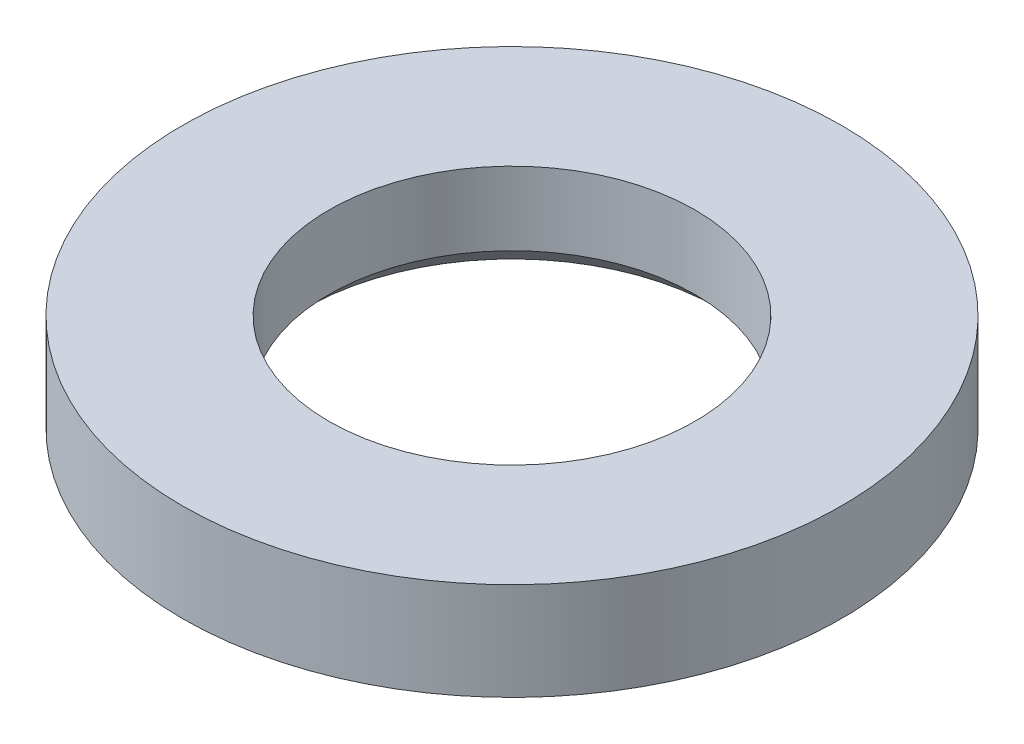
SolidWorks part; units mm, degrees
ref_plane "Front Plane" through (0, 0, 0) normal (0, 0, 1) x (1, 0, 0)
ref_plane "Top Plane" through (0, 0, 0) normal (0, 1, 0) x (1, 0, 0)
ref_plane "Right Plane" through (0, 0, 0) normal (1, 0, 0) x (0, 0, -1)
sketch "Sketch1" plane through (0, 0, 0) normal (0, 0, 1) x (1, 0, 0)
  line L0 (1.5, 0) -> (2.7, 0)
  line L1 (2.7, 0) -> (2.7, 0.8)
  line L2 (2.7, 0.8) -> (1.5, 0.8)
  line L5 (1.5, 0.8) -> (1.5, 0)
  line L6 (0, 0) -> (0, 3.2) construction
  point P6 (0, 0)
  point P9 (0, 0)
  dimension "D2" = 0.8
  dimension "D3" = 3
  dimension "D5" = 1.2
revolve "Revolve1" add sketch "Sketch1" angle 360 about L6
chamfer "Chamfer1" distance 0.2 angle 45 1 edges at (0, 0, -1.5)
